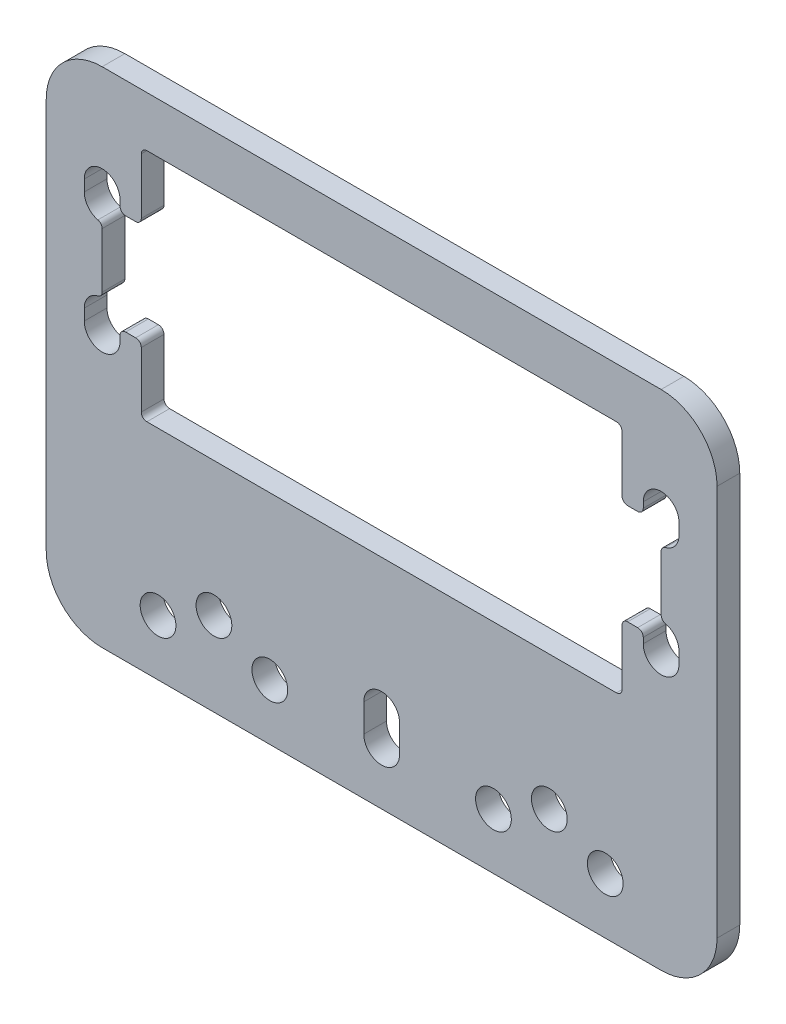
SolidWorks part; units mm, degrees
ref_plane "Front Plane" through (0, 0, 0) normal (0, 0, 1) x (1, 0, 0)
ref_plane "Top Plane" through (0, 0, 0) normal (0, 1, 0) x (1, 0, 0)
ref_plane "Right Plane" through (0, 0, 0) normal (1, 0, 0) x (0, 0, -1)
sketch "Sketch1" plane through (0, 0, 0) normal (0, 0, 1) x (1, 0, 0)
  line L1 (-30, -22.5) -> (30, -22.5)
  line L2 (-30, -22.5) -> (-30, 22.5)
  line L3 (-30, 22.5) -> (30, 22.5)
  line L4 (30, -22.5) -> (30, 22.5)
  line L5 (-30, -22.5) -> (30, 22.5) construction
  line L6 (-30, 22.5) -> (30, -22.5) construction
  point P0 (0, 0)
  dimension "D1" = 60
  dimension "D2" = 45
extrude "Boss-Extrude1" add sketch "Sketch1" along normal blind 2.032
fillet "Fillet1" radius 5 4 edges at (-30, -22.5, 1.016) (30, -22.5, 1.016) (-30, 22.5, 1.016) (30, 22.5, 1.016)
sketch "Sketch2" plane through (0, 0, 2.032) normal (0, 0, 1) x (1, 0, 0)
  line L0 (-41.2577, -7.5) -> (43.7202, -7.5) construction
  line L1 (-25, -22.5) -> (25, -22.5) construction
  line L2 (0, -54.6431) -> (0, 54.6431) construction
  line L3 (-20.5, -3) -> (20.5, -3)
  line L4 (-20.5, -3) -> (-20.5, 18)
  line L5 (-20.5, 18) -> (20.5, 18)
  line L6 (20.5, -3) -> (20.5, 18)
  line L7 (-20.5, -3) -> (20.5, 18) construction
  line L8 (-20.5, 18) -> (20.5, -3) construction
  line L9 (-33.3183, 7.5) -> (35.3128, 7.5) construction
  line L10 (25, 22.5) -> (-25, 22.5) construction
  point P4 (0, 7.5)
  dimension "D1" = 15
  dimension "D2" = 21
  dimension "D3" = 41
extrude "Cut-Extrude1" cut sketch "Sketch2" against normal through all
fillet "Fillet2" radius 0.5 4 edges at (20.5, 18, 1.016) (20.5, -3, 1.016) (-20.5, -3, 1.016) (-20.5, 18, 1.016)
sketch "Sketch3" plane through (0, 0, 2.032) normal (0, 0, 1) x (1, 0, 0)
  line L0 (-25, 3) -> (-25, 2) construction
  line L1 (-23.4, 3) -> (-23.4, 2)
  line L2 (-26.6, 3) -> (-26.6, 2)
  line L3 (-20.5, 7.5) -> (20.5, 7.5) construction
  line L4 (-20.5, 17.5) -> (-20.5, -2.5) construction
  line L5 (20.5, -2.5) -> (20.5, 17.5) construction
  line L6 (0, 18.6557) -> (0, -3.4503) construction
  line L7 (0, -54.6431) -> (0, 54.6431) construction
  line L8 (-25, 12) -> (-25, 13) construction
  line L9 (-23.4, 12) -> (-23.4, 13)
  line L10 (-26.6, 12) -> (-26.6, 13)
  line L11 (25, 3) -> (25, 2) construction
  line L12 (23.4, 3) -> (23.4, 2)
  line L13 (26.6, 3) -> (26.6, 2)
  line L14 (25, 12) -> (25, 13) construction
  line L15 (23.4, 12) -> (23.4, 13)
  line L16 (26.6, 12) -> (26.6, 13)
  arc A0 (-23.4, 3) -> (-26.6, 3) centre (-25, 3) ccw
  arc A1 (-26.6, 2) -> (-23.4, 2) centre (-25, 2) ccw
  arc A2 (-23.4, 12) -> (-26.6, 12) centre (-25, 12) cw
  arc A3 (-26.6, 13) -> (-23.4, 13) centre (-25, 13) cw
  arc A4 (23.4, 3) -> (26.6, 3) centre (25, 3) cw
  arc A5 (26.6, 2) -> (23.4, 2) centre (25, 2) cw
  arc A6 (23.4, 12) -> (26.6, 12) centre (25, 12) ccw
  arc A7 (26.6, 13) -> (23.4, 13) centre (25, 13) ccw
  point P2 (-25, 2.5)
  point P20 (-25, 12.5)
  point P27 (25, 2.5)
  point P34 (25, 12.5)
  dimension "D1" = 10
  dimension "D2" = 50
  dimension "D3" = 3.2
  dimension "D4" = 1
extrude "Cut-Extrude2" cut sketch "Sketch3" against normal through all
sketch "Sketch4" plane through (0, 0, 2.032) normal (0, 0, 1) x (1, 0, 0)
  line L0 (0, -54.6431) -> (0, 54.6431) construction
  line L1 (-30, -15) -> (30, -15) construction
  line L2 (-30, 17.5) -> (-30, -17.5) construction
  line L3 (30, -17.5) -> (30, 17.5) construction
  line L4 (-25, -22.5) -> (25, -22.5) construction
  line L5 (0, 0) -> (0, -6.6395) construction
  line L6 (-30, -17.5) -> (30, -17.5) construction
  line L7 (0, -15) -> (0, -17.5) construction
  line L8 (1.6, -15) -> (1.6, -17.5)
  line L9 (-1.6, -15) -> (-1.6, -17.5)
  circle A0 centre (-15, -15) radius 1.6
  circle A1 centre (0, -15) radius 1.6 construction
  circle A2 centre (15, -15) radius 1.6
  circle A3 centre (-22.5, -15) radius 1.6 construction
  circle A4 centre (-7.5, -15) radius 1.6 construction
  circle A5 centre (7.5, -15) radius 1.6 construction
  circle A6 centre (22.5, -15) radius 1.6 construction
  circle A7 centre (0, -17.5) radius 1.6 construction
  circle A8 centre (10, -17.5) radius 1.6
  circle A9 centre (-10, -17.5) radius 1.6
  circle A10 centre (20, -17.5) radius 1.6
  circle A11 centre (-20, -17.5) radius 1.6
  arc A12 (1.6, -15) -> (-1.6, -15) centre (0, -15) ccw
  arc A13 (-1.6, -17.5) -> (1.6, -17.5) centre (0, -17.5) ccw
  point P39 (0, -16.25)
  dimension "D1" = 3.2
  dimension "D2" = 7.5
  dimension "D3" = 15
  dimension "D4" = 15
  dimension "D5" = 15
  dimension "D6" = 7.5
  dimension "D7" = 5
  dimension "D8" = 10
  dimension "D9" = 10
  dimension "D10" = 10
extrude "Cut-Extrude3" cut sketch "Sketch4" against normal through all
sketch "Sketch5" plane through (0, 0, 2.032) normal (0, 0, 1) x (1, 0, 0)
  line L0 (0, 18) -> (0, -3) construction
  line L1 (20, 18) -> (-20, 18) construction
  line L2 (-20, -3) -> (20, -3) construction
  line L3 (-32.3401, 7.5) -> (31.7632, 7.5) construction
  line L4 (-21, -3) -> (21, -3)
  line L5 (-21.5, -2.5) -> (-21.5, 3)
  line L6 (-21, 18) -> (21, 18)
  line L7 (21.5, -2.5) -> (21.5, 3)
  line L8 (-21.5, -3) -> (21.5, 18) construction
  line L9 (-21.0398, 17.7752) -> (21.5, -3) construction
  line L10 (20.5, -2.5) -> (20.5, 17.5) construction
  line L11 (21.5, 12) -> (23.4, 12)
  line L12 (25, 10.4) -> (25, 4.6)
  line L13 (23.4, 3) -> (21.5, 3)
  line L14 (21.5, 12) -> (21.5, 17.5)
  line L15 (-23.4, 3) -> (-21.5, 3)
  line L16 (-25, 10.4) -> (-25, 4.6)
  line L17 (-21.5, 12) -> (-23.4, 12)
  line L18 (-21.5, 12) -> (-21.5, 17.5)
  arc A0 (21, -3) -> (21.5, -2.5) centre (21, -2.5) ccw
  arc A1 (-21, -3) -> (-21.5, -2.5) centre (-21, -2.5) cw
  arc A2 (-21.5, 17.5) -> (-21, 18) centre (-21, 17.5) cw
  arc A3 (21, 18) -> (21.5, 17.5) centre (21, 17.5) cw
  arc A4 (-25, 10.4) -> (-23.4, 12) centre (-23.4, 10.4) cw
  arc A5 (-23.4, 3) -> (-25, 4.6) centre (-23.4, 4.6) cw
  arc A6 (25, 4.6) -> (23.4, 3) centre (23.4, 4.6) cw
  arc A7 (23.4, 12) -> (25, 10.4) centre (23.4, 10.4) cw
  arc A8 (-26.6, 12) -> (-23.4, 12) centre (-25, 12) ccw construction
  point P6 (0, 7.5)
  point P37 (-25, 12)
  point P40 (-25, 3)
  point P43 (25, 3)
  point P46 (25, 12)
  dimension "D1" = 0.5
  dimension "D2" = 1
extrude "Cut-Extrude4" cut sketch "Sketch5" against normal through all
fillet "Fillet3" radius 0.5 12 edges at (-21.5, 12, 1.016) (-23.4, 12, 1.016) (-25, 10.4, 1.016) (-25, 4.6, 1.016) (-21.5, 3, 1.016) (-23.4, 3, 1.016) (21.5, 3, 1.016) (23.4, 3, 1.016) (25, 4.6, 1.016) (25, 10.4, 1.016) (23.4, 12, 1.016) (21.5, 12, 1.016)
sketch "Alignment_Sketch" plane through (0, 0, 0) normal (0, 0, -1) x (-1, 0, 0)
  line L0 (-15, -15) -> (15, -15) construction
  point P0 (-15, -15)
  point P1 (15, -15)
